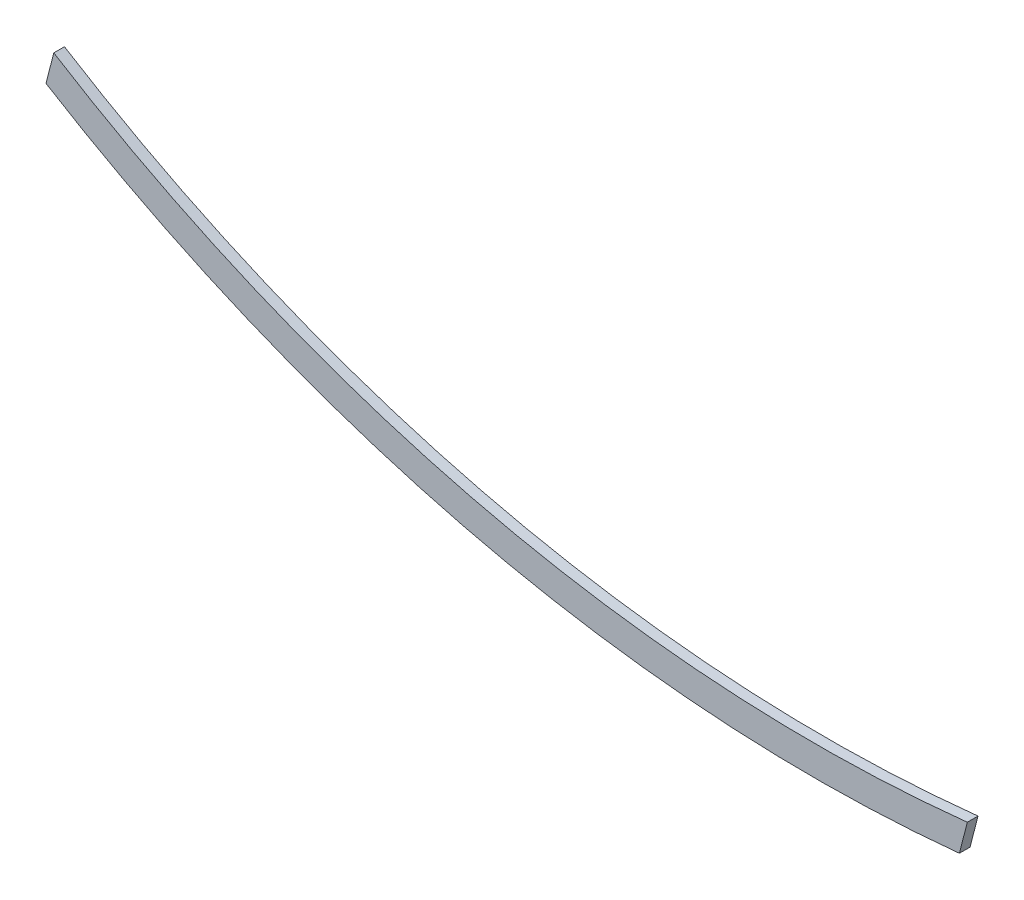
SolidWorks part; units mm, degrees
ref_plane "Front Plane" through (0, 0, 0) normal (0, 0, 1) x (1, 0, 0)
ref_plane "Top Plane" through (0, 0, 0) normal (0, 1, 0) x (1, 0, 0)
ref_plane "Right Plane" through (0, 0, 0) normal (1, 0, 0) x (0, 0, -1)
sketch "Sketch1" plane through (0, 0, 0) normal (0, 0, 1) x (1, 0, 0)
  line L1 (105.4811, -60.6005) -> (142.5209, 83.9577)
  line L2 (402.8922, 1290.379) -> (42.9885, -114.2453) construction
  line L4 (-4134.4102, 1064.709) -> (-4170.821, 922.6056)
  line L5 (-3229.481, 3511.4744) -> (-3589.3847, 2106.8502) construction
  arc A3 (-5.898, 69.7511) -> (142.5209, 83.9577) centre (-573.1934, 6778.7694) ccw
  arc A4 (-5.898, 69.7511) -> (-3985.8657, 974.7692) centre (-573.1934, 6778.7694) cw
  arc A5 (-3985.8657, 974.7692) -> (-4134.4102, 1064.709) centre (-573.1934, 6778.7694) cw
  arc A6 (5.898, -69.7511) -> (105.4811, -60.6005) centre (-573.1934, 6778.7694) ccw
  arc A7 (5.898, -69.7511) -> (-4056.8261, 854.0852) centre (-573.1934, 6778.7694) cw
  arc A8 (-4056.8261, 854.0852) -> (-4170.821, 922.6056) centre (-573.1934, 6778.7694) cw
extrude "Boss-Extrude1" add sketch "Sketch1" along normal blind 50
